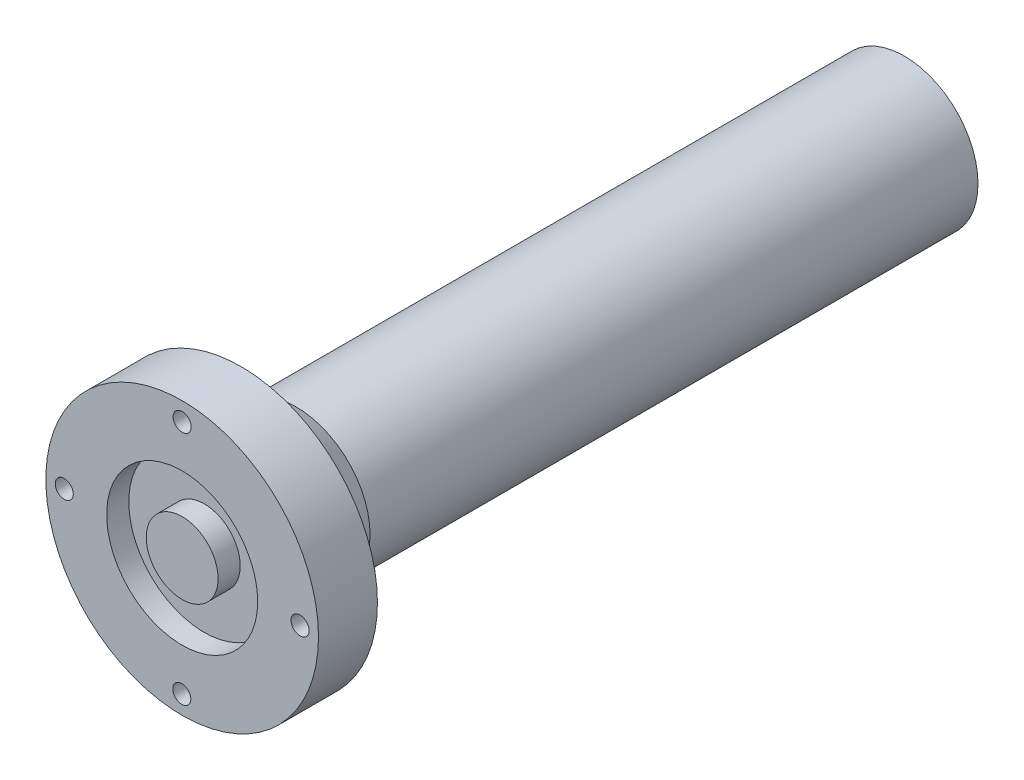
SolidWorks part; units mm, degrees
ref_plane "정면" through (0, 0, 0) normal (0, 0, 1) x (1, 0, 0)
ref_plane "윗면" through (0, 0, 0) normal (0, 1, 0) x (1, 0, 0)
ref_plane "우측면" through (0, 0, 0) normal (1, 0, 0) x (0, 0, -1)
sketch "스케치1" plane through (0, 0, 0) normal (0, 0, 1) x (1, 0, 0)
  circle A0 centre (0, 0) radius 20
  dimension "D1" = 40
extrude "보스-돌출1" add sketch "스케치1" along normal blind 180
sketch "스케치3" plane through (0, 0, 180) normal (0, 0, 1) x (1, 0, 0)
  circle A0 centre (0, 0) radius 37
  dimension "D1" = 74
extrude "보스-돌출3" add sketch "스케치3" along normal blind 16
sketch "스케치4" plane through (0, 0, 196) normal (0, 0, 1) x (1, 0, 0)
  circle A0 centre (0, 0) radius 20.5
  dimension "D1" = 41
extrude "컷-돌출1" cut sketch "스케치4" against normal blind 6
sketch "스케치5" plane through (0, 0, 190) normal (0, 0, 1) x (1, 0, 0)
  line L0 (0, 46.2137) -> (0, -49.0664) construction
  line L1 (0, 0) -> (47.2122, 0) construction
  line L2 (47.2122, 0) -> (-61.0478, 0) construction
  circle A0 centre (0, 0) radius 9.75
  dimension "D1" = 19.5
extrude "보스-돌출4" add sketch "스케치5" along normal blind 6
sketch "스케치10" plane through (0, 0, 196) normal (0, 0, 1) x (1, 0, 0)
  line L2 (0, 0) -> (50.7174, 0) construction
  line L3 (50.7174, 0) -> (-47.4732, 0) construction
  line L4 (0, 32) -> (0, -40.9427) construction
  circle A0 centre (0, 32) radius 2.45
  circle A1 centre (32, 0.1503) radius 2.45
  circle A2 centre (-32, 0.2584) radius 2.45
  circle A3 centre (-0.1081, -32) radius 2.45
  dimension "D1" = 4.9
  dimension "D2" = 32
  dimension "D3" = 32
  dimension "D4" = 32
  dimension "D5" = 32
extrude "컷-돌출3" cut sketch "스케치10" against normal up to next
sketch "스케치18" plane through (0, 0, 180) normal (0, 0, -1) x (-1, 0, 0)
  circle A0 centre (0, 32) radius 4.4
  circle A1 centre (32, 0.2584) radius 4.4
  circle A2 centre (0.1081, -32) radius 4.4
  circle A3 centre (-32, 0.1503) radius 4.4
  dimension "D1" = 8.8
extrude "컷-돌출4" cut sketch "스케치18" against normal blind 5
sketch "스케치20" plane through (0, 0, 0) normal (0, 1, 0) x (1, 0, 0)
  line L0 (-20, -180) -> (-27.6, -180)
  line L1 (-27.6, -180) -> (-36.4, -180) construction
  line L2 (37, -180) -> (-37, -180) construction
  line L3 (-27.6, -180) -> (-20, -165)
  line L4 (-20, 0) -> (-20, -180) construction
  line L5 (-20, -165) -> (-20, -180)
  line L6 (0, -180) -> (0, -98) construction
  dimension "D1" = 15
revolve "회전1" add sketch "스케치20" angle 360 about L6
